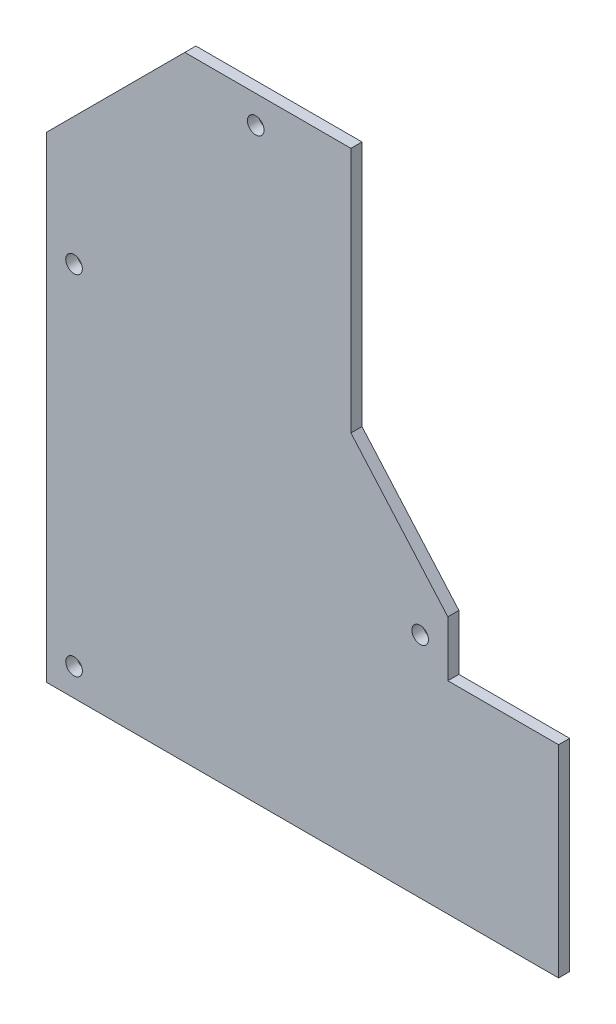
SolidWorks part; units mm, degrees
ref_plane "前视基准面" through (0, 0, 0) normal (0, 0, 1) x (1, 0, 0)
ref_plane "上视基准面" through (0, 0, 0) normal (0, 1, 0) x (1, 0, 0)
ref_plane "右视基准面" through (0, 0, 0) normal (1, 0, 0) x (0, 0, -1)
sketch "草图1" plane through (0, 0, 0) normal (0, 0, 1) x (1, 0, 0)
  line L18 (-85, -75) -> (100, -75)
  line L19 (100, -75) -> (100, -2.0318)
  line L20 (100, -2.0318) -> (60, -2.0318)
  line L21 (60, -2.0318) -> (60, 17.9682)
  line L22 (60, 17.9682) -> (25, 57.9682)
  line L23 (25, 57.9682) -> (25, 147)
  line L24 (25, 147) -> (-35, 147)
  line L25 (-35, 147) -> (-85, 97)
  line L26 (-85, 97) -> (-85, -75)
extrude "凸台-拉伸1" add sketch "草图1" along normal blind 4
sketch "草图2" plane through (0, 0, 0) normal (0, 0, -1) x (-1, 0, 0)
  circle A0 centre (75, -65) radius 3
  circle A1 centre (-50, 7.3322) radius 3
  circle A2 centre (9.3934, 137) radius 3
  circle A3 centre (75, 60.7868) radius 3
  circle A4 centre (75, 60.7868) radius 3 construction
  circle A5 centre (75, -65) radius 3 construction
  circle A6 centre (9.3934, 137) radius 3 construction
  circle A7 centre (-50, 7.3322) radius 3 construction
extrude "切除-拉伸1" cut sketch "草图2" against normal blind 10
